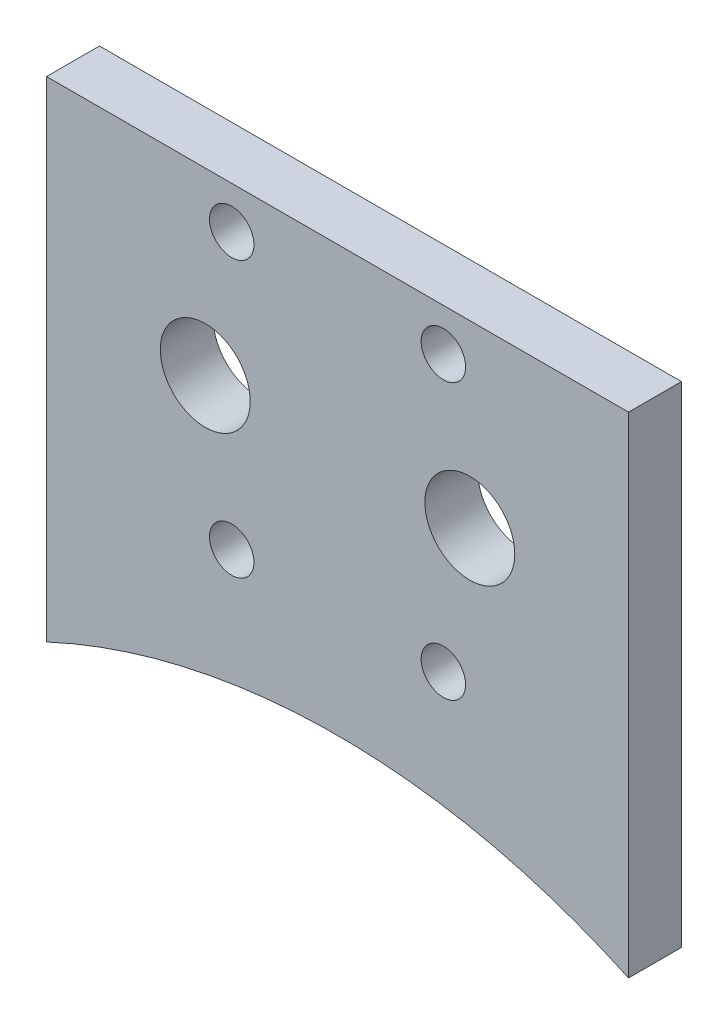
SolidWorks part; units mm, degrees
ref_plane "Front Plane" through (0, 0, 0) normal (0, 0, 1) x (1, 0, 0)
ref_plane "Top Plane" through (0, 0, 0) normal (0, 1, 0) x (1, 0, 0)
ref_plane "Right Plane" through (0, 0, 0) normal (1, 0, 0) x (0, 0, -1)
sketch "Sketch1" plane through (0, 0, 0) normal (0, 0, 1) x (1, 0, 0)
  line L0 (-50.4176, -29.8314) -> (-27.4176, -29.8314)
  line L5 (27.5824, -29.8314) -> (50.5824, -29.8314)
  line L6 (50.5824, -29.8314) -> (50.5824, 25.1686)
  line L7 (45.5824, 30.1686) -> (-45.4176, 30.1686)
  line L8 (-50.4176, 25.1686) -> (-50.4176, -29.8314)
  arc A0 (27.5824, -29.8314) -> (-27.4176, -29.8314) centre (0.0824, -88.7275) ccw
  arc A1 (50.5824, 25.1686) -> (45.5824, 30.1686) centre (45.5824, 25.1686) ccw
  arc A2 (-45.4176, 30.1686) -> (-50.4176, 25.1686) centre (-45.4176, 25.1686) ccw
  circle A3 centre (12.5824, -0.5199) radius 4.25
  circle A4 centre (10.0824, -13.5199) radius 2.1
  circle A5 centre (-9.9176, -13.5199) radius 2.1
  circle A6 centre (-12.4176, -0.5199) radius 4.25
  circle A7 centre (-9.9176, 12.4801) radius 2.1
  circle A8 centre (10.0824, 12.4801) radius 2.1
extrude "Boss-Extrude1" add sketch "Sketch1" along normal blind 5
sketch "Sketch2" plane through (0, 0, 5) normal (0, 0, 1) x (1, 0, 0)
  line L0 (0.0824, 16.4801) -> (0.0824, 33.7046) construction
  line L1 (-50.4176, 30.1686) -> (-27.4176, 30.1686)
  line L2 (-50.4176, 30.1686) -> (-50.4176, -29.8314)
  line L3 (-50.4176, -29.8314) -> (-27.4176, -29.8314)
  line L4 (-27.4176, 30.1686) -> (-27.4176, -29.8314)
  line L5 (-50.4176, 30.1686) -> (-27.4176, -29.8314) construction
  line L6 (-50.4176, -29.8314) -> (-27.4176, 30.1686) construction
  line L7 (18.5824, 16.4801) -> (-18.4176, 16.4801) construction
  line L8 (50.5824, -29.8314) -> (27.5824, 30.1686) construction
  line L9 (50.5824, 30.1686) -> (27.5824, -29.8314) construction
  line L10 (27.5824, 30.1686) -> (27.5824, -29.8314)
  line L11 (50.5824, -29.8314) -> (27.5824, -29.8314)
  line L12 (50.5824, 30.1686) -> (50.5824, -29.8314)
  line L13 (50.5824, 30.1686) -> (27.5824, 30.1686)
  point P4 (-38.9176, 0.1686)
  point P14 (39.0824, 0.1686)
extrude "Cut-Extrude1" cut sketch "Sketch2" against normal blind 10
fillet "Fillet1" radius 5 1 edges at (27.5824, 30.1686, 2.5)
fillet "Fillet2" radius 5 1 edges at (-27.4176, 30.1686, 2.5)
sketch "Sketch3" plane through (0, 0, 0) normal (0, 0, -1) x (-1, 0, 0)
  line L0 (-27.5824, 25.1686) -> (-27.5824, -29.8314) construction
  line L1 (-22.5824, 30.1686) -> (22.4176, 30.1686) construction
  line L2 (27.4176, -29.8314) -> (27.4176, 25.1686) construction
  line L3 (-27.5824, 25.1686) -> (-27.5824, 16.4801)
  line L4 (-22.5824, 30.1686) -> (22.4176, 30.1686)
  line L5 (27.4176, 16.4448) -> (27.4176, 25.1686)
  line L6 (27.4176, 16.4448) -> (-27.5824, 16.4801)
  line L7 (43.4176, 16.4801) -> (-43.5824, 16.4801) construction
  arc A0 (-22.5824, 30.1686) -> (-27.5824, 25.1686) centre (-22.5824, 25.1686) ccw construction
  arc A1 (27.4176, 25.1686) -> (22.4176, 30.1686) centre (22.4176, 25.1686) ccw construction
  arc A2 (-22.5824, 30.1686) -> (-27.5824, 25.1686) centre (-22.5824, 25.1686) ccw
  arc A3 (27.4176, 25.1686) -> (22.4176, 30.1686) centre (22.4176, 25.1686) ccw
extrude "Cut-Extrude2" cut sketch "Sketch3" against normal blind 5
